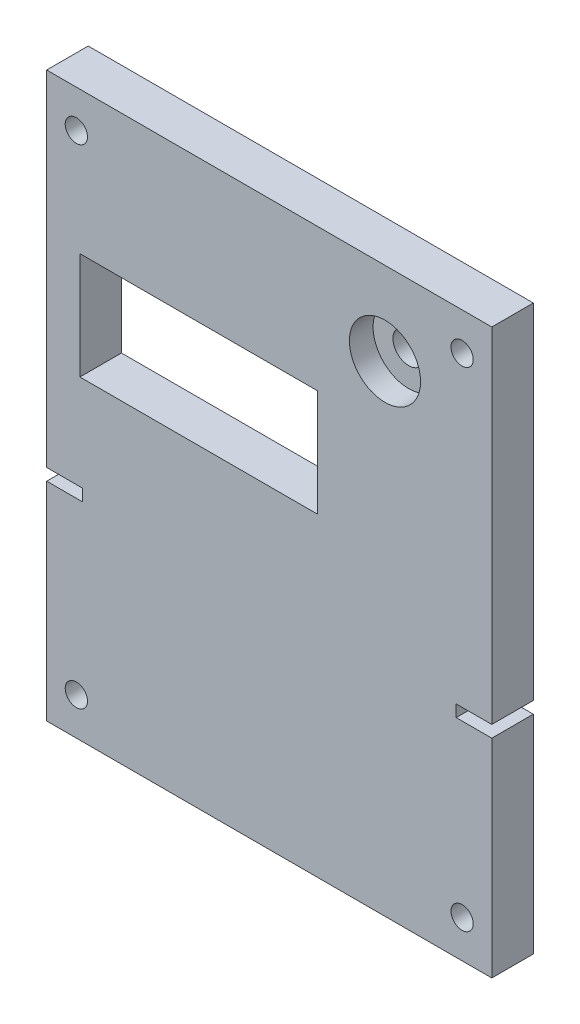
SolidWorks part; units mm, degrees
ref_plane "Front Plane" through (0, 0, 0) normal (0, 0, 1) x (1, 0, 0)
ref_plane "Top Plane" through (0, 0, 0) normal (0, 1, 0) x (1, 0, 0)
ref_plane "Right Plane" through (0, 0, 0) normal (1, 0, 0) x (0, 0, -1)
sketch "Sketch1" plane through (0, 0, 0) normal (0, 0, 1) x (1, 0, 0)
  line L1 (-47.625, -60.325) -> (47.625, -60.325)
  line L2 (-47.625, -60.325) -> (-47.625, 60.325)
  line L3 (-47.625, 60.325) -> (47.625, 60.325)
  line L4 (47.625, -60.325) -> (47.625, 60.325)
  line L5 (-47.625, -60.325) -> (47.625, 60.325) construction
  line L6 (-47.625, 60.325) -> (47.625, -60.325) construction
  point P0 (0, 0)
  dimension "D1" = 120.65
  dimension "D2" = 95.25
extrude "Boss-Extrude1" add sketch "Sketch1" along normal blind 8.89
sketch "Sketch2" plane through (0, 0, 8.89) normal (0, 0, 1) x (1, 0, 0)
  line L0 (47.625, 60.325) -> (-47.625, 60.325) construction
  line L1 (-47.625, -60.325) -> (47.625, -60.325)
  line L2 (-47.625, -60.325) -> (-47.625, 60.325)
  line L3 (-47.625, 60.325) -> (47.625, 60.325)
  line L4 (47.625, -60.325) -> (47.625, 60.325)
  line L5 (-47.625, -60.325) -> (47.625, 60.325) construction
  line L6 (-47.625, 60.325) -> (47.625, -60.325) construction
  line L7 (47.625, -60.325) -> (47.625, 60.325) construction
  line L9 (36.195, -52.2817) -> (-36.195, -52.2817) construction
  line L10 (41.275, -47.2017) -> (41.275, 47.2017) construction
  line L11 (36.195, 52.2817) -> (-36.195, 52.2817) construction
  line L12 (-41.275, -47.2017) -> (-41.275, 47.2017) construction
  line L13 (41.275, -52.2817) -> (-41.275, 52.2817) construction
  line L14 (41.275, 52.2817) -> (-41.275, -52.2817) construction
  arc A0 (-41.275, 47.2017) -> (-36.195, 52.2817) centre (-41.275, 52.2817) ccw construction
  arc A1 (36.195, 52.2817) -> (41.275, 47.2017) centre (41.275, 52.2817) ccw construction
  arc A2 (41.275, -47.2017) -> (36.195, -52.2817) centre (41.275, -52.2817) ccw construction
  arc A3 (-36.195, -52.2817) -> (-41.275, -47.2017) centre (-41.275, -52.2817) ccw construction
  circle A4 centre (-41.275, 52.2817) radius 2.3812
  circle A5 centre (41.275, 52.2817) radius 2.3812
  circle A6 centre (41.275, -52.2817) radius 2.3812
  circle A7 centre (-41.275, -52.2817) radius 2.3812
  point P0 (0, 0)
  point P10 (0, 0)
  dimension "D2" = 5.08
  dimension "D3" = 4.7625
  dimension "D1" = 6.35
extrude "Cut-Extrude2" cut sketch "Sketch2" against normal through all flip side to cut
ref_plane "Plane1" through (0, 0, 8.89) normal (0, 0, 1) x (1, 0, 0)
sketch "Sketch3" plane through (0, 0, 8.89) normal (0, 0, 1) x (1, 0, 0)
  line L0 (47.625, -60.325) -> (47.625, 60.325) construction
  line L1 (47.625, 60.325) -> (-47.625, 60.325) construction
  circle A0 centre (24.765, 42.545) radius 7.62
  dimension "D1" = 15.24
  dimension "D2" = 22.86
  dimension "D3" = 17.78
extrude "Cut-Extrude3" cut sketch "Sketch3" against normal blind 5.08 contours A0
sketch "Sketch4" plane through (0, 0, 3.81) normal (0, 0, 1) x (1, 0, 0)
  circle A0 centre (24.765, 42.545) radius 3.3655
  dimension "D1" = 6.731
extrude "Cut-Extrude4" cut sketch "Sketch4" against normal through all
sketch "Sketch5" plane through (0, 0, 8.89) normal (0, 0, 1) x (1, 0, 0)
  line L0 (47.625, 60.325) -> (-47.625, 60.325) construction
  line L1 (-40.513, 29.845) -> (10.287, 29.845)
  line L2 (-40.513, 29.845) -> (-40.513, 6.985)
  line L3 (-40.513, 6.985) -> (10.287, 6.985)
  line L4 (10.287, 29.845) -> (10.287, 6.985)
  line L5 (-40.513, 29.845) -> (10.287, 6.985) construction
  line L6 (-40.513, 6.985) -> (10.287, 29.845) construction
  line L7 (-47.625, 60.325) -> (-47.625, -60.325) construction
  point P0 (-15.113, 18.415)
  dimension "D1" = 41.91
  dimension "D2" = 50.8
  dimension "D3" = 22.86
  dimension "D4" = 32.512
extrude "Cut-Extrude5" cut sketch "Sketch5" against normal through all
ref_plane "Plane2" through (0, 0, 8.89) normal (0, 0, 1) x (1, 0, 0)
sketch "Sketch6" plane through (0, 0, 8.89) normal (0, 0, 1) x (1, 0, 0)
  line L0 (-47.625, -13.335) -> (-40.005, -13.335)
  line L1 (-47.625, 60.325) -> (-47.625, -60.325) construction
  line L2 (-40.005, -13.335) -> (-40.005, -15.875)
  line L3 (-40.005, -15.875) -> (-47.625, -15.875)
  line L4 (-47.625, -15.875) -> (-47.625, -13.335)
  line L5 (47.625, -13.335) -> (40.005, -13.335)
  line L6 (47.625, -60.325) -> (47.625, 60.325) construction
  line L7 (40.005, -13.335) -> (40.005, -15.875)
  line L8 (40.005, -15.875) -> (47.625, -15.875)
  line L9 (47.625, -15.875) -> (47.625, -13.335)
  line L10 (-40.513, 6.985) -> (10.287, 6.985) construction
  dimension "D1" = 7.62
  dimension "D2" = 2.54
  dimension "D3" = 20.32
extrude "Cut-Extrude6" cut sketch "Sketch6" against normal through all
